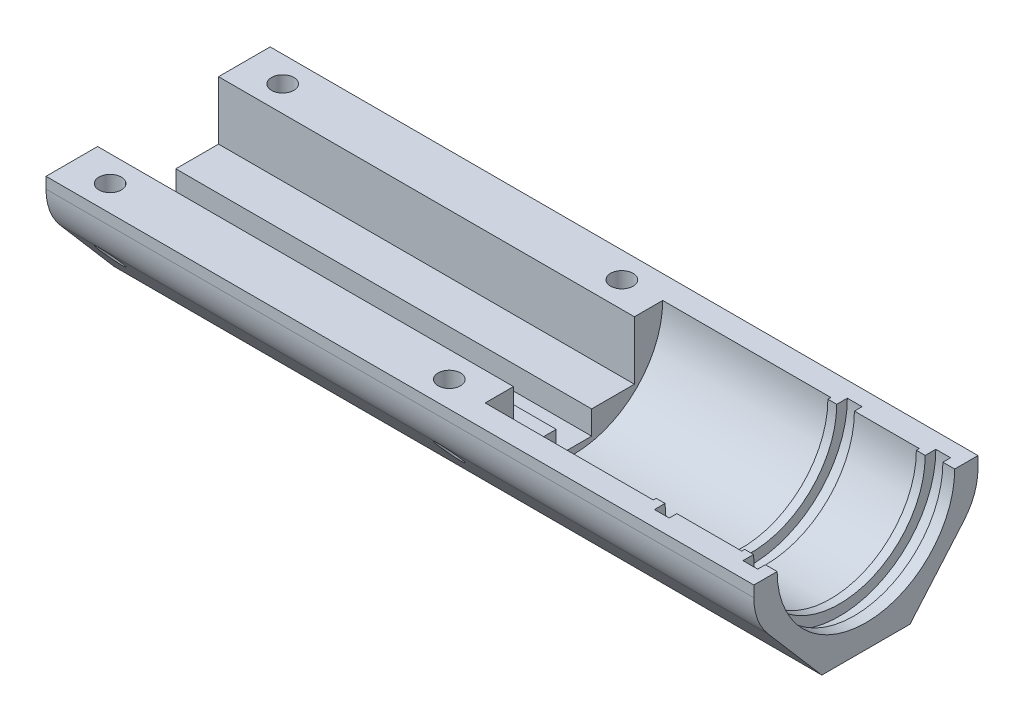
SolidWorks part; units mm, degrees
ref_plane "Plan de face" through (0, 0, 0) normal (0, 0, 1) x (1, 0, 0)
ref_plane "Plan de dessus" through (0, 0, 0) normal (0, 1, 0) x (1, 0, 0)
ref_plane "Plan de droite" through (0, 0, 0) normal (1, 0, 0) x (0, 0, -1)
sketch "Esquisse1" plane through (0, 0, 0) normal (0, 0, 1) x (1, 0, 0)
  line L0 (0, 0) -> (51.3556, 0) construction
  line L2 (70.5, -15.05) -> (99, -15.05)
  line L3 (0, -15.05) -> (0, -25.05)
  line L4 (0, -25.05) -> (120, -25.05)
  line L5 (120, -15.05) -> (120, -25.05)
  line L6 (100.5, -15.05) -> (100.5, -16.35)
  line L7 (100.5, -16.35) -> (103, -16.35)
  line L8 (103, -15.05) -> (103, -16.35)
  line L10 (115.5, -15.05) -> (115.5, -16.35)
  line L11 (115.5, -16.35) -> (118, -16.35)
  line L12 (118, -15.05) -> (118, -16.35)
  line L13 (103, -15.05) -> (114, -15.05)
  line L15 (115.5, -15.05) -> (115.5, -14.55)
  line L16 (115.5, -14.55) -> (114, -14.55)
  line L17 (114, -15.05) -> (114, -14.55)
  line L19 (100.5, -15.05) -> (100.5, -14.55)
  line L20 (100.5, -14.55) -> (99, -14.55)
  line L21 (99, -15.05) -> (99, -14.55)
  line L22 (118, -15.05) -> (120, -15.05)
  line L25 (0, -15.05) -> (0, -9.55)
  line L26 (0, -9.55) -> (70.5, -9.55)
  line L27 (70.5, -15.05) -> (70.5, -9.55)
  point P27 (100.5, -15.7)
  dimension "D1" = 1.3
  dimension "D2" = 2
  dimension "16.5" = 16.35
  dimension "2.5" = 2.5
  dimension "D3" = 10
  dimension "15" = 15
  dimension "D4" = 120
  dimension "D5" = 15.5
  dimension "0.5" = 0.5
  dimension "1.5" = 1.5
  dimension "30" = 30
revolve "Révolution1" add sketch "Esquisse1" angle 180 mid plane about L0
sketch "Esquisse2" plane through (0, 0, 0) normal (0, 1, 0) x (1, 0, 0)
  line L1 (120, -25.05) -> (0, -25.05)
  line L2 (120, -25.05) -> (120, 25.05)
  line L3 (120, 25.05) -> (0, 25.05)
  line L4 (0, -25.05) -> (0, 25.05)
extrude "Enlèv. mat.-Extru.1" cut sketch "Esquisse2" against normal blind 10 from offset 19 offset against normal yes
sketch "Esquisse3" plane through (0, 0, 0) normal (0, 0, 1) x (1, 0, 0)
  line L1 (-16.5972, 11.9449) -> (129.8412, 11.9449)
  line L2 (-16.5972, 11.9449) -> (-16.5972, -38.3667)
  line L3 (-16.5972, -38.3667) -> (129.8412, -38.3667)
  line L4 (129.8412, 11.9449) -> (129.8412, -38.3667)
  point P4 (129.8412, 11.9449)
extrude "Enlèv. mat.-Extru.2" cut sketch "Esquisse3" against normal blind 10 from offset 19 offset against normal yes
ref_plane "Plan1" through (0, -16.3249, -19) normal (0, -0.6517, -0.7585) x (-1, 0, 0)
sketch "Esquisse4" plane through (0, -16.3249, -19) normal (0, -0.6517, -0.7585) x (-1, 0, 0)
  line L1 (-132.0168, 19.4165) -> (24.0432, 19.4165)
  line L2 (-132.0168, 19.4165) -> (-132.0168, -23.7377)
  line L3 (-132.0168, -23.7377) -> (24.0432, -23.7377)
  line L4 (24.0432, 19.4165) -> (24.0432, -23.7377)
extrude "Enlèv. mat.-Extru.3" cut sketch "Esquisse4" against normal blind 7
mirror "Symétrie1" about plane through (0, 0, 0) normal (0, 0, 1) of "Enlèv. mat.-Extru.3", "Enlèv. mat.-Extru.2"
fillet "Congé1" radius 10 2 edges at (60, -5.5836, -19) (60, -5.5836, 19)
sketch "Esquisse5" plane through (0, 0, 0) normal (-1, 0, 0) x (0, 0, 1)
  line L0 (9.55, 0) -> (19, 0) construction
  line L1 (10.25, 0) -> (-10.25, 0)
  line L2 (10.25, 0) -> (10.25, -9.9)
  line L3 (10.25, -9.9) -> (3, -9.9)
  line L4 (-10.25, 0) -> (-10.25, -9.9)
  line L5 (0, -13.9) -> (0, 0) construction
  line L7 (-3, -9.9) -> (-3, -13.9)
  line L8 (-3, -13.9) -> (3, -13.9)
  line L9 (3, -9.9) -> (3, -13.9)
  line L10 (-3, -9.9) -> (-10.25, -9.9)
  dimension "D1" = 9.9
  dimension "D2" = 20.5
  dimension "D3" = 4
  dimension "D4" = 6
extrude "Enlèv. mat.-Extru.4" cut sketch "Esquisse5" against normal through all
sketch "Esquisse6" plane through (0, 0, 0) normal (0, 1, 0) x (1, 0, 0)
  line L0 (0, 14.625) -> (64, 14.625) construction
  line L3 (0, 10.25) -> (0, 19) construction
  line L4 (0, 10.25) -> (70.5, 10.25) construction
  line L5 (70.5, 15.05) -> (70.5, 10.25) construction
  circle A0 centre (6.5, 14.625) radius 1.9
  circle A1 centre (64, 14.625) radius 1.9
  dimension "D1" = 3.8
  dimension "D2" = 6.5
  dimension "D3" = 6.5
extrude "Enlèv. mat.-Extru.5" cut sketch "Esquisse6" against normal through all
mirror "Symétrie2" about plane through (0, 0, 0) normal (0, 0, 1) of "Enlèv. mat.-Extru.5"
